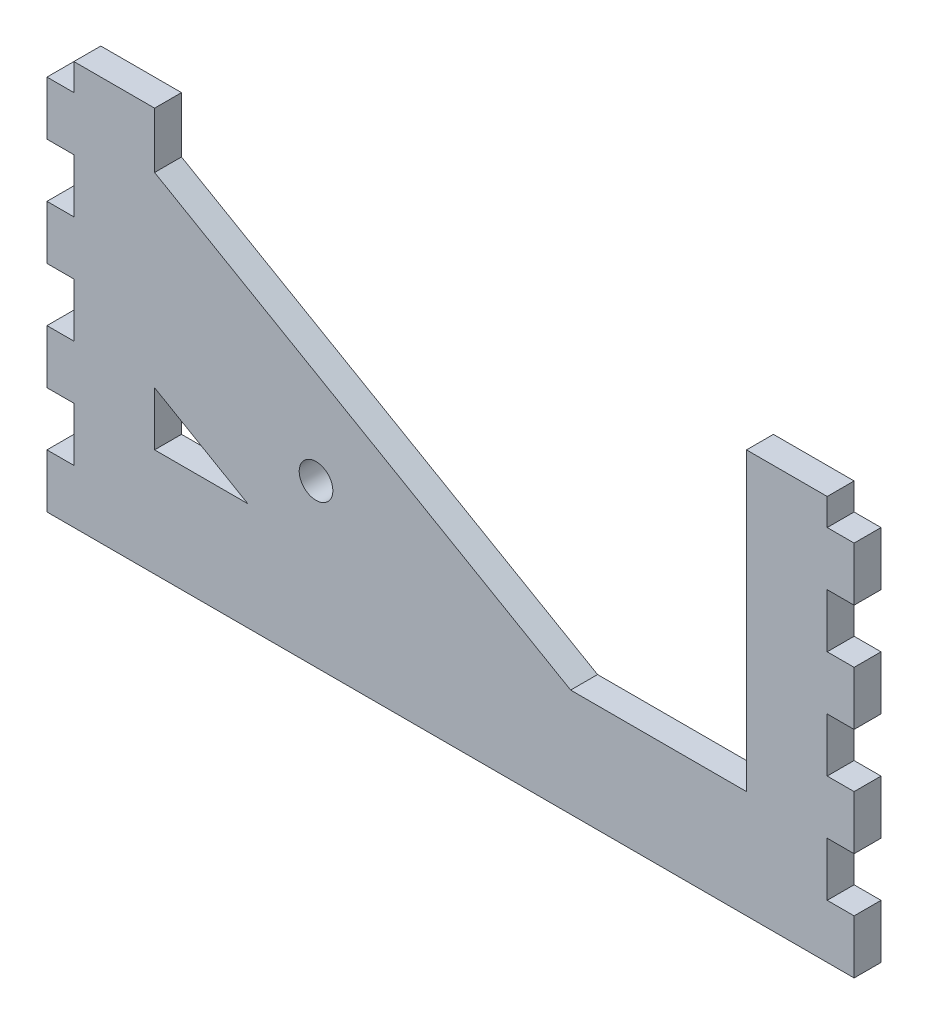
SolidWorks part; units mm, degrees
material "Pine"
ref_plane "Front Plane" through (0, 0, 0) normal (0, 0, 1) x (1, 0, 0)
ref_plane "Top Plane" through (0, 0, 0) normal (0, 1, 0) x (1, 0, 0)
ref_plane "Right Plane" through (0, 0, 0) normal (1, 0, 0) x (0, 0, -1)
sketch "Sketch1" plane through (0, 0, 0) normal (0, 0, 1) x (1, 0, 0)
  line L1 (0, 0) -> (190.5, 0)
  line L2 (0, 0) -> (0, 95.25)
  line L3 (0, 95.25) -> (190.5, 95.25)
  line L4 (190.5, 0) -> (190.5, 95.25)
  dimension "D1" = 190.5
  dimension "D2" = 95.25
extrude "Boss-Extrude1" add sketch "Sketch1" along normal blind 6.35
sketch "Sketch2" plane through (0, 0, 6.35) normal (0, 0, 1) x (1, 0, 0)
  line L0 (0, 95.25) -> (0, 0) construction
  line L1 (0, 0) -> (190.5, 0) construction
  circle A0 centre (63.5, 38.1) radius 3.9687
  dimension "D3" = 7.9375
  dimension "D1" = 63.5
  dimension "D2" = 38.1
extrude "Cut-Extrude1" cut sketch "Sketch2" against normal through all
sketch "Sketch3" plane through (0, 0, 6.35) normal (0, 0, 1) x (1, 0, 0)
  line L0 (0, 95.25) -> (0, 0) construction
  line L1 (0, 12.7) -> (6.35, 12.7)
  line L2 (0, 12.7) -> (0, 25.4)
  line L3 (0, 25.4) -> (6.35, 25.4)
  line L4 (6.35, 12.7) -> (6.35, 25.4)
  dimension "D1" = 6.35
  dimension "D2" = 12.7
  dimension "D3" = 12.7
extrude "Cut-Extrude2" cut sketch "Sketch3" against normal through all
sketch "Sketch4" plane through (0, 0, 6.35) normal (0, 0, 1) x (1, 0, 0)
  line L0 (190.5, 0) -> (190.5, 95.25) construction
  line L1 (190.5, 12.7) -> (184.15, 12.7)
  line L2 (190.5, 12.7) -> (190.5, 25.4)
  line L3 (190.5, 25.4) -> (184.15, 25.4)
  line L4 (184.15, 12.7) -> (184.15, 25.4)
  line L5 (6.35, 12.7) -> (6.35, 25.4) construction
  line L6 (0, 12.7) -> (6.35, 12.7) construction
extrude "Cut-Extrude3" cut sketch "Sketch4" against normal through all
pattern_linear "LPattern1" count 4 spacing 25.4 along (0, 1, 0) of "Cut-Extrude2", "Cut-Extrude3"
sketch "Sketch6" plane through (0, 0, 6.35) normal (0, 0, 1) x (1, 0, 0)
  line L0 (25.4, 95.25) -> (25.4, 82.0941)
  line L1 (184.15, 95.25) -> (6.35, 95.25) construction
  line L2 (25.4, 82.0941) -> (123.597, 25.4)
  line L3 (123.597, 25.4) -> (165.1, 25.4)
  line L4 (165.1, 25.4) -> (165.1, 95.25)
  line L9 (165.1, 95.25) -> (25.4, 95.25)
  line L10 (25.4, 38.1) -> (25.4, 25.4)
  line L11 (25.4, 25.4) -> (47.397, 25.4)
  line L12 (47.397, 25.4) -> (25.4, 38.1)
  line L13 (6.35, 88.9) -> (6.35, 95.25) construction
  line L14 (0, 0) -> (190.5, 0) construction
  line L15 (184.15, 50.8) -> (184.15, 38.1) construction
  circle A0 centre (63.5, 38.1) radius 3.9687 construction
  dimension "D5" = 19.05
  dimension "D1" = 19.05
  dimension "D2" = 19.05
  dimension "D3" = 120
  dimension "D4" = 25.4
  dimension "D6" = 19.05
extrude "Cut-Extrude4" cut sketch "Sketch6" against normal through all
